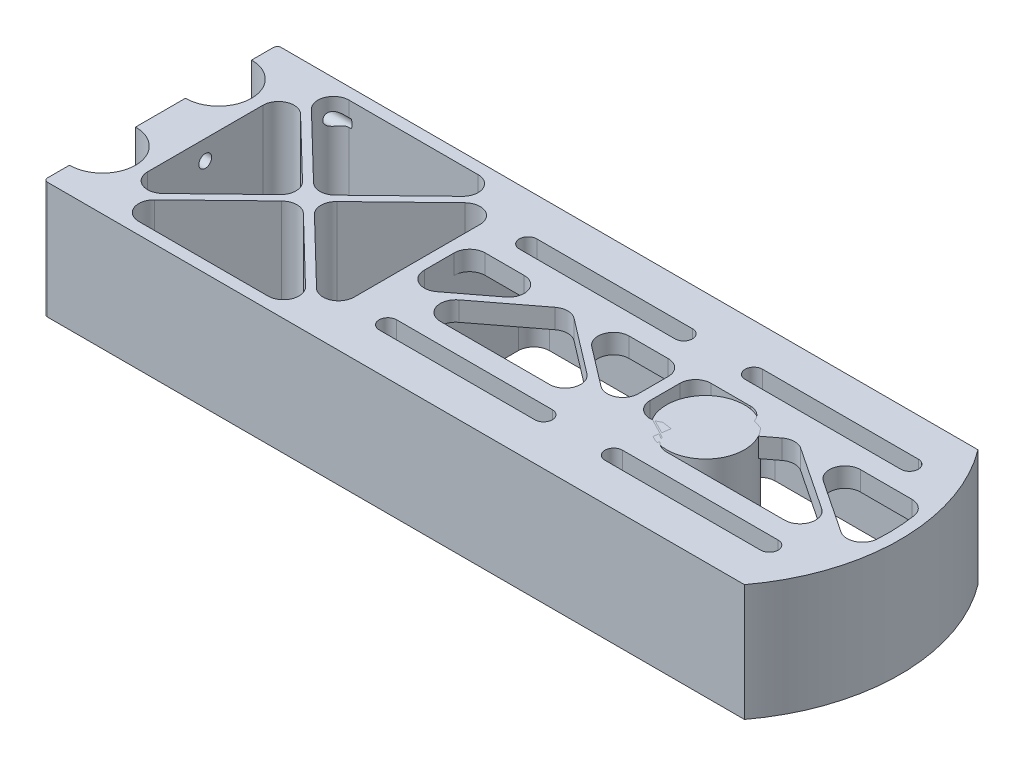
SolidWorks part; units mm, degrees
material "3.1355 (EN-AW 2024)"
ref_plane "Front" through (0, 0, 0) normal (0, 0, 1) x (1, 0, 0)
ref_plane "Top" through (0, 0, 0) normal (0, 1, 0) x (1, 0, 0)
ref_plane "Right" through (0, 0, 0) normal (1, 0, 0) x (0, 0, -1)
sketch "Эскиз1" plane through (0, 0, 0) normal (0, 1, 0) x (1, 0, 0)
  line L0 (0, 0) -> (0, 60) construction
  line L1 (0, 60) -> (180, 60)
  line L2 (190, 60) -> (190, 0) construction
  line L3 (190, 0) -> (180, 0) construction
  line L4 (0, 30) -> (140, 30) construction
  line L5 (0, 60) -> (0, 52)
  line L6 (0, 37.8) -> (0, 22.2)
  line L7 (0, 8) -> (0, 0)
  line L8 (140, 30) -> (190, 30) construction
  line L9 (180, 60) -> (190, 60) construction
  line L10 (180, 0) -> (0, 0)
  circle A0 centre (0, 44.9) radius 7.1 construction
  circle A1 centre (0, 15.1) radius 7.1 construction
  arc A2 (0, 52) -> (0, 37.8) centre (0, 44.9) cw
  arc A3 (0, 8) -> (0, 22.2) centre (0, 15.1) ccw
  arc A4 (180, 0) -> (180, 60) centre (140, 30) ccw
  point P11 (0, 52)
  point P12 (0, 37.8)
  dimension "D2" = 14.2
  dimension "D4" = 29.8
  dimension "D8" = 50
  dimension "D1" = 60
  dimension "D3" = 15.1
  dimension "D5" = 140
  dimension "D6" = 50
  dimension "D7" = 190
extrude "Бобышка-Вытянуть1" add sketch "Эскиз1" along normal blind 30
sketch "Эскиз2" plane through (0, 30, 0) normal (0, 1, 0) x (1, 0, 0)
  line L5 (3, 3) -> (178.4708, 3)
  line L6 (3, 3) -> (178.4708, 3)
  line L12 (3, 5.4558) -> (3, 3)
  line L15 (178.4708, 57) -> (3, 57)
  line L16 (3, 57) -> (3, 54.5442)
  line L17 (3, 35.2558) -> (3, 24.7442)
  line L18 (3, 5.4558) -> (3, 3)
  line L21 (178.4708, 57) -> (3, 57)
  line L22 (3, 57) -> (3, 54.5442)
  line L23 (3, 35.2558) -> (3, 24.7442)
  arc A3 (178.4708, 3) -> (178.4708, 57) centre (140, 30) ccw
  arc A4 (3, 35.2558) -> (3, 54.5442) centre (0, 44.9) ccw
  arc A5 (3, 5.4558) -> (3, 24.7442) centre (0, 15.1) ccw
  arc A6 (3, 35.2558) -> (3, 54.5442) centre (0, 44.9) ccw
  arc A7 (3, 5.4558) -> (3, 24.7442) centre (0, 15.1) ccw
  arc A8 (178.4708, 3) -> (178.4708, 57) centre (140, 30) ccw
  dimension "D1" = 3
extrude "Вырез-Вытянуть1" cut sketch "Эскиз2" against normal through all
sketch "Temp" plane through (0, 30, 0) normal (0, 1, 0) x (1, 0, 0)
  circle A0 centre (140, 30) radius 10
  dimension "D1" = 20
extrude "Бобышка-Вытянуть2" add sketch "Temp" against normal up to surface (30 mm away) separate body up to face at (49.7088, 0, -30)
sketch "Эскиз3" plane through (0, 30, 0) normal (0, 1, 0) x (1, 0, 0)
  line L0 (178.4708, 57) -> (3, 57) construction
  line L1 (174.4166, 48) -> (134.4166, 48) construction
  line L2 (174.4166, 43.5) -> (134.4166, 43.5)
  line L3 (174.4166, 52.5) -> (134.4166, 52.5)
  line L4 (174.4166, 48) -> (183.4166, 48) construction
  line L5 (125.4166, 57) -> (125.4166, 30) construction
  line L6 (0, 30) -> (140, 30) construction
  line L7 (76.4166, 48) -> (116.4166, 48) construction
  line L8 (76.4166, 43.5) -> (116.4166, 43.5)
  line L9 (76.4166, 52.5) -> (116.4166, 52.5)
  line L10 (187, 30) -> (125.4166, 30) construction
  line L11 (76.4166, 12) -> (116.4166, 12) construction
  line L12 (76.4166, 16.5) -> (116.4166, 16.5)
  line L13 (76.4166, 7.5) -> (116.4166, 7.5)
  line L14 (174.4166, 12) -> (134.4166, 12) construction
  line L15 (174.4166, 16.5) -> (134.4166, 16.5)
  line L16 (174.4166, 7.5) -> (134.4166, 7.5)
  line L17 (68.9166, 57) -> (68.9166, 40.5)
  line L18 (68.9166, 40.5) -> (185.8121, 40.5)
  line L19 (178.4708, 57) -> (68.9166, 57)
  line L20 (76.4166, 12) -> (116.4166, 12) construction
  line L21 (76.4166, 16.5) -> (116.4166, 16.5)
  line L22 (76.4166, 7.5) -> (116.4166, 7.5)
  line L23 (174.4166, 12) -> (134.4166, 12) construction
  line L24 (174.4166, 16.5) -> (134.4166, 16.5)
  line L25 (174.4166, 7.5) -> (134.4166, 7.5)
  line L26 (68.9166, 19.5) -> (185.8121, 19.5)
  line L27 (178.4708, 3) -> (68.9166, 3)
  line L28 (68.9166, 3) -> (68.9166, 19.5)
  arc A0 (174.4166, 43.5) -> (174.4166, 52.5) centre (174.4166, 48) ccw
  arc A1 (134.4166, 52.5) -> (134.4166, 43.5) centre (134.4166, 48) ccw
  arc A2 (178.4708, 3) -> (178.4708, 57) centre (140, 30) ccw construction
  arc A3 (76.4166, 43.5) -> (76.4166, 52.5) centre (76.4166, 48) cw
  arc A4 (116.4166, 52.5) -> (116.4166, 43.5) centre (116.4166, 48) cw
  arc A5 (76.4166, 16.5) -> (76.4166, 7.5) centre (76.4166, 12) ccw
  arc A6 (116.4166, 7.5) -> (116.4166, 16.5) centre (116.4166, 12) ccw
  arc A7 (174.4166, 16.5) -> (174.4166, 7.5) centre (174.4166, 12) cw
  arc A8 (134.4166, 7.5) -> (134.4166, 16.5) centre (134.4166, 12) cw
  arc A9 (185.8121, 40.5) -> (178.4708, 57) centre (140, 30) ccw
  arc A10 (76.4166, 16.5) -> (76.4166, 7.5) centre (76.4166, 12) ccw
  arc A11 (116.4166, 7.5) -> (116.4166, 16.5) centre (116.4166, 12) ccw
  arc A12 (174.4166, 16.5) -> (174.4166, 7.5) centre (174.4166, 12) cw
  arc A13 (134.4166, 7.5) -> (134.4166, 16.5) centre (134.4166, 12) cw
  arc A14 (185.8121, 19.5) -> (178.4708, 3) centre (140, 30) cw
  point P1 (154.4166, 48)
  point P20 (96.4166, 48)
  point P28 (96.4166, 12)
  point P35 (154.4166, 12)
  arc M3 (178.4708, 57) -> (178.4708, 3) centre (140, 30) cw
  line M4 (178.4708, 3) -> (3, 3)
  line M10 (3, 57) -> (178.4708, 57)
  dimension "D1" = 4.5
  dimension "D6" = 3
  dimension "D2" = 40
  dimension "D3" = 9
  dimension "D4" = 9
  dimension "D5" = 9
  dimension "D7" = 7.5
extrude "Бобышка-Вытянуть3" add sketch "Эскиз3" against normal blind 5 contours L17 L18 A1 L3 A0 L2 L9 A4 L8 A3 M3 M10 | L28 L26 A6 L13 A5 L12 L16 A8 L15 A7 M4 M3
sketch "Эскиз4" plane through (0, 30, 0) normal (0, 1, 0) x (1, 0, 0)
  line L0 (3, 57) -> (3, 54.5442) construction
  line L1 (3, 35.2558) -> (3, 24.7442) construction
  line L2 (3, 5.4558) -> (3, 3) construction
  line L3 (3, 3) -> (68.9166, 3) construction
  line L4 (68.9166, 57) -> (3, 57) construction
  line L5 (3, 57) -> (3, 54.5442)
  line L6 (3, 35.2558) -> (3, 24.7442)
  line L7 (3, 5.4558) -> (3, 3)
  line L8 (3, 3) -> (10.1, 3)
  line L9 (10.1, 57) -> (3, 57)
  line L10 (10.1, 57) -> (10.1, 3)
  arc A0 (3, 35.2558) -> (3, 54.5442) centre (0, 44.9) ccw construction
  arc A1 (3, 5.4558) -> (3, 24.7442) centre (0, 15.1) ccw construction
  arc A2 (3, 35.2558) -> (3, 54.5442) centre (0, 44.9) ccw
  arc A3 (3, 5.4558) -> (3, 24.7442) centre (0, 15.1) ccw
  line M4 (68.9166, 3) -> (3, 3)
  line M5 (3, 3) -> (3, 5.4558)
  arc M6 (3, 5.4558) -> (3, 24.7442) centre (0, 15.1) ccw
  line M7 (3, 24.7442) -> (3, 35.2558)
  arc M8 (3, 35.2558) -> (3, 54.5442) centre (0, 44.9) ccw
  line M9 (3, 54.5442) -> (3, 57)
  line M10 (3, 57) -> (68.9166, 57)
extrude "Бобышка-Вытянуть4" add sketch "Эскиз4" against normal through all contours L10 M10 M9 M8 | L10 M8 M7 M6 | L10 M6 M5 M4
sketch "Эскиз6" plane through (0, 30, 0) normal (0, 1, 0) x (1, 0, 0)
  line L0 (65.9166, 57) -> (65.9166, 3)
  line L1 (68.9166, 57) -> (10.1, 57) construction
  line L2 (10.1, 3) -> (68.9166, 3) construction
  line L3 (68.9166, 57) -> (68.9166, 40.5) construction
  line L4 (65.9166, 3) -> (68.9166, 3)
  line L5 (68.9166, 3) -> (68.9166, 57)
  line L6 (68.9166, 57) -> (65.9166, 57)
  dimension "D1" = 3
extrude "Бобышка-Вытянуть5" add sketch "Эскиз6" against normal through all
sketch "Эскиз7" plane through (0, 30, 0) normal (0, 1, 0) x (1, 0, 0)
  line L0 (10.1, 3) -> (65.9166, 57) construction
  line L1 (10.1, 57) -> (65.9166, 3) construction
  line L2 (10.1, 55.6086) -> (36.5701, 30)
  line L3 (11.5382, 3) -> (38.0083, 28.6086)
  line L4 (11.5382, 57) -> (38.0083, 31.3914)
  line L5 (10.1, 4.3914) -> (36.5701, 30)
  line L6 (65.9166, 57) -> (10.1, 57) construction
  line L7 (10.1, 57) -> (10.1, 3) construction
  line L8 (10.1, 3) -> (65.9166, 3) construction
  line L9 (65.9166, 57) -> (65.9166, 3) construction
  line L10 (65.9166, 57) -> (64.4784, 57)
  line L11 (10.1, 57) -> (10.1, 55.6086)
  line L12 (10.1, 3) -> (11.5382, 3)
  line L13 (65.9166, 57) -> (65.9166, 55.6086)
  line L14 (11.5382, 57) -> (10.1, 57)
  line L15 (10.7953, 57.7187) -> (66.6119, 3.7187) construction
  line L16 (9.4047, 56.2813) -> (65.2213, 2.2813) construction
  line L17 (65.9166, 4.3914) -> (65.9166, 3)
  line L18 (9.4047, 3.7187) -> (65.2213, 57.7187) construction
  line L19 (10.7953, 2.2813) -> (66.6119, 56.2813) construction
  line L20 (64.4784, 3) -> (65.9166, 3)
  line L21 (10.1, 4.3914) -> (10.1, 3)
  line L22 (39.4465, 30) -> (65.9166, 55.6086)
  line L23 (39.4465, 30) -> (65.9166, 4.3914)
  line L24 (38.0083, 31.3914) -> (64.4784, 57)
  line L25 (38.0083, 28.6086) -> (64.4784, 3)
  dimension "D1" = 1
  dimension "D2" = 1
extrude "Бобышка-Вытянуть6" add sketch "Эскиз7" against normal through all
sketch "Эскиз9" plane through (0, 25, 0) normal (0, -1, 0) x (1, 0, 0)
  line L0 (120.9166, -12) -> (129.9166, -12) construction
  line L1 (125.4166, -3) -> (125.4166, -57) construction
  line L2 (68.9166, -57) -> (178.4708, -57) construction
  line L3 (123.9166, -3) -> (123.9166, -57)
  line L4 (101.5292, -3) -> (68.9166, -3) construction
  line L5 (126.9166, -3) -> (126.9166, -57)
  line L6 (123.9166, -3) -> (126.9166, -3)
  line L7 (123.9166, -57) -> (126.9166, -57)
  arc A0 (116.4166, -16.5) -> (116.4166, -7.5) centre (116.4166, -12) ccw construction
  arc A1 (134.4166, -16.5) -> (134.4166, -7.5) centre (134.4166, -12) ccw construction
  point P8 (125.4166, -12)
  dimension "D1" = 1.5
  dimension "D2" = 1.5
extrude "Бобышка-Вытянуть8" add sketch "Эскиз9" along normal through all and the other way through all
sketch "Эскиз8" plane through (0, 30, 0) normal (0, 1, 0) x (1, 0, 0)
  line L0 (96.4166, 43.5) -> (96.4166, 16.5) construction
  line L1 (76.4166, 43.5) -> (116.4166, 43.5) construction
  line L2 (76.4166, 16.5) -> (116.4166, 16.5) construction
  line L3 (154.4166, 43.5) -> (154.4166, 16.5) construction
  line L4 (174.4166, 43.5) -> (134.4166, 43.5) construction
  line L5 (174.4166, 16.5) -> (134.4166, 16.5) construction
  line L6 (68.9166, 19.5) -> (96.4166, 40.5) construction
  line L7 (116.4166, 48) -> (134.4166, 48) construction
  line L8 (125.4166, 48) -> (125.4166, 19.5) construction
  line L9 (68.9166, 40.5) -> (123.9166, 40.5) construction
  line L10 (96.4166, 40.5) -> (123.9166, 19.5) construction
  line L11 (126.9166, 19.5) -> (154.4401, 40.4052) construction
  line L12 (154.4401, 40.4052) -> (185.8121, 19.5) construction
  line L13 (70.5643, 19.5) -> (96.4166, 39.2418)
  line L14 (96.4166, 39.2418) -> (122.2689, 19.5)
  line L15 (128.5699, 19.5) -> (154.478, 39.1782)
  line L16 (154.478, 39.1782) -> (184.0088, 19.5)
  line L17 (68.9166, 20.7582) -> (94.7689, 40.5)
  line L18 (98.0643, 40.5) -> (123.9166, 20.7582)
  line L19 (126.9166, 20.7557) -> (152.9116, 40.5)
  line L20 (122.2689, 19.5) -> (123.9166, 19.5)
  line L22 (94.7689, 40.5) -> (98.0643, 40.5)
  line L23 (68.9166, 19.5) -> (68.9166, 40.5) construction
  line L24 (68.9166, 19.5) -> (123.9166, 19.5) construction
  line L25 (123.9166, 19.5) -> (123.9166, 40.5) construction
  line L26 (126.9166, 40.5) -> (126.9166, 19.5) construction
  line L27 (126.9166, 40.5) -> (185.8121, 40.5) construction
  line L28 (126.9166, 19.5) -> (185.8121, 19.5) construction
  line L29 (68.9166, 19.5) -> (68.9166, 20.7582)
  line L30 (68.9166, 19.5) -> (70.5643, 19.5)
  line L31 (123.9166, 19.5) -> (123.9166, 20.7582)
  line L32 (126.9166, 20.7557) -> (126.9166, 19.5)
  line L33 (152.9116, 40.5) -> (156.1011, 40.5)
  line L34 (126.9166, 19.5) -> (128.5699, 19.5)
  line L35 (184.0088, 19.5) -> (185.8121, 19.5)
  line L36 (154.4021, 41.6321) -> (186.3666, 20.3322) construction
  line L37 (154.478, 39.1782) -> (185.2576, 18.6678) construction
  line L38 (156.1011, 40.5) -> (186.0401, 20.5497)
  line L39 (127.5214, 18.7037) -> (154.478, 39.1782) construction
  line L40 (126.3117, 20.2963) -> (154.4021, 41.6321) construction
  line L42 (96.4166, 41.7582) -> (124.5235, 20.2948) construction
  line L43 (68.3097, 20.2948) -> (96.4166, 41.7582) construction
  line L44 (69.5235, 18.7052) -> (96.4166, 39.2418) construction
  line L45 (96.4166, 39.2418) -> (123.3097, 18.7052) construction
  arc A1 (185.8121, 19.5) -> (185.8121, 40.5) centre (140, 30) ccw construction
  arc A2 (185.8121, 19.5) -> (186.0401, 20.5497) centre (140, 30) ccw
  point P26 (69.5235, 18.7052)
  point P27 (96.4324, 39.2539)
  point P28 (125.4324, 18.2539)
  point P30 (185.2357, 18.6828)
  point P31 (68.3097, 20.2948)
  point P32 (96.4007, 41.7461)
  point P33 (125.4007, 20.7461)
  point P34 (154.3931, 42.8858)
  point P35 (186.3885, 20.3172)
  point P49 (154.4166, 40.5)
  dimension "D1" = 1
  dimension "D2" = 1
extrude "Бобышка-Вытянуть7" add sketch "Эскиз8" against normal up to surface (5 mm away) up to face at (96.4166, 25, -12)
fillet "Скругление1" radius 4 10 edges at (11.5382, 15, -57) (38.0083, 15, -31.3914) (64.4784, 15, -57) (65.9166, 15, -55.6086) (39.4465, 15, -30) (65.9166, 15, -4.3914) (11.5382, 15, -3) (64.4784, 15, -3) (38.0083, 15, -28.6086) (36.5701, 15, -30)
fillet "Скругление2" radius 4 8 edges at (178.4708, 12.5, -57) (178.4708, 12.5, -3) (126.9166, 12.5, -3) (126.9166, 12.5, -57) (123.9166, 12.5, -3) (68.9166, 12.5, -3) (68.9166, 12.5, -57) (123.9166, 12.5, -57)
fillet "Скругление3" radius 4 18 edges at (98.0643, 27.5, -40.5) (123.9166, 27.5, -40.5) (123.9166, 27.5, -20.7582) (122.2689, 27.5, -19.5) (96.4166, 27.5, -39.2418) (70.5643, 27.5, -19.5) (94.7689, 27.5, -40.5) (68.9166, 27.5, -40.5) (68.9166, 27.5, -20.7582) (185.8121, 27.5, -40.5) (156.1011, 27.5, -40.5) (186.0401, 27.5, -20.5497) (184.0088, 27.5, -19.5) (154.478, 27.5, -39.1782) (128.5699, 27.5, -19.5) (126.9166, 27.5, -20.7557) (152.9116, 27.5, -40.5) (126.9166, 27.5, -40.5)
sketch "Эскиз10" plane through (0, 30, 0) normal (0, 1, 0) x (1, 0, 0)
  line L90 (76.4166, 52.5) -> (116.4166, 52.5) construction
  line L91 (76.4166, 43.5) -> (116.4166, 43.5) construction
  line L92 (116.4166, 50.25) -> (76.4166, 50.25)
  line L93 (76.4166, 45.75) -> (116.4166, 45.75)
  line L94 (116.4166, 50.25) -> (76.4166, 50.25)
  line L95 (76.4166, 45.75) -> (116.4166, 45.75)
  line L96 (76.4166, 52.5) -> (116.4166, 52.5)
  line L97 (76.4166, 43.5) -> (116.4166, 43.5)
  line L98 (174.4166, 52.5) -> (134.4166, 52.5) construction
  line L99 (174.4166, 43.5) -> (134.4166, 43.5) construction
  line L100 (174.4166, 52.5) -> (134.4166, 52.5)
  line L101 (174.4166, 43.5) -> (134.4166, 43.5)
  line L102 (76.4166, 16.5) -> (116.4166, 16.5) construction
  line L103 (76.4166, 7.5) -> (116.4166, 7.5) construction
  line L104 (76.4166, 16.5) -> (116.4166, 16.5)
  line L105 (76.4166, 7.5) -> (116.4166, 7.5)
  line L106 (174.4166, 16.5) -> (134.4166, 16.5) construction
  line L107 (174.4166, 7.5) -> (134.4166, 7.5) construction
  line L108 (174.4166, 16.5) -> (134.4166, 16.5)
  line L109 (174.4166, 7.5) -> (134.4166, 7.5)
  line L110 (174.4166, 45.75) -> (134.4166, 45.75)
  line L111 (174.4166, 50.25) -> (134.4166, 50.25)
  line L112 (174.4166, 14.25) -> (134.4166, 14.25)
  line L113 (174.4166, 9.75) -> (134.4166, 9.75)
  line L114 (76.4166, 9.75) -> (116.4166, 9.75)
  line L115 (76.4166, 14.25) -> (116.4166, 14.25)
  arc A90 (76.4166, 52.5) -> (76.4166, 43.5) centre (76.4166, 48) ccw construction
  arc A91 (116.4166, 43.5) -> (116.4166, 52.5) centre (116.4166, 48) ccw construction
  arc A92 (76.4166, 50.25) -> (76.4166, 45.75) centre (76.4166, 48) ccw
  arc A93 (116.4166, 45.75) -> (116.4166, 50.25) centre (116.4166, 48) ccw
  arc A94 (76.4166, 50.25) -> (76.4166, 45.75) centre (76.4166, 48) ccw
  arc A95 (116.4166, 45.75) -> (116.4166, 50.25) centre (116.4166, 48) ccw
  arc A96 (76.4166, 52.5) -> (76.4166, 43.5) centre (76.4166, 48) ccw
  arc A97 (116.4166, 43.5) -> (116.4166, 52.5) centre (116.4166, 48) ccw
  arc A98 (134.4166, 52.5) -> (134.4166, 43.5) centre (134.4166, 48) ccw construction
  arc A99 (174.4166, 43.5) -> (174.4166, 52.5) centre (174.4166, 48) ccw construction
  arc A100 (134.4166, 52.5) -> (134.4166, 43.5) centre (134.4166, 48) ccw
  arc A101 (174.4166, 43.5) -> (174.4166, 52.5) centre (174.4166, 48) ccw
  arc A102 (116.4166, 7.5) -> (116.4166, 16.5) centre (116.4166, 12) ccw construction
  arc A103 (76.4166, 16.5) -> (76.4166, 7.5) centre (76.4166, 12) ccw construction
  arc A104 (116.4166, 7.5) -> (116.4166, 16.5) centre (116.4166, 12) ccw
  arc A105 (76.4166, 16.5) -> (76.4166, 7.5) centre (76.4166, 12) ccw
  arc A106 (134.4166, 16.5) -> (134.4166, 7.5) centre (134.4166, 12) ccw construction
  arc A107 (174.4166, 7.5) -> (174.4166, 16.5) centre (174.4166, 12) ccw construction
  arc A108 (134.4166, 16.5) -> (134.4166, 7.5) centre (134.4166, 12) ccw
  arc A109 (174.4166, 7.5) -> (174.4166, 16.5) centre (174.4166, 12) ccw
  arc A110 (134.4166, 50.25) -> (134.4166, 45.75) centre (134.4166, 48) ccw
  arc A111 (174.4166, 45.75) -> (174.4166, 50.25) centre (174.4166, 48) ccw
  arc A112 (134.4166, 14.25) -> (134.4166, 9.75) centre (134.4166, 12) ccw
  arc A113 (174.4166, 9.75) -> (174.4166, 14.25) centre (174.4166, 12) ccw
  arc A114 (76.4166, 14.25) -> (76.4166, 9.75) centre (76.4166, 12) ccw
  arc A115 (116.4166, 9.75) -> (116.4166, 14.25) centre (116.4166, 12) ccw
  dimension "D1" = 2.25
  dimension "D2" = 2.25
  dimension "D3" = 2.25
  dimension "D4" = 2.25
extrude "Бобышка-Вытянуть9" add sketch "Эскиз10" against normal up to surface (5 mm away) up to face at (155.2427, 25, -27.7696)
sketch "Эскиз12" plane through (0, 0, 0) normal (0, -1, 0) x (1, 0, 0)
  line L0 (5, -23.8755) -> (5, -36.1245)
  line L1 (0, -37.8) -> (0, -22.2) construction
  line L2 (10.1, -55.6086) -> (10.1, -4.3914) construction
  line L3 (10.1, -44.9) -> (10.1, -15.1)
  arc A6 (0, -25.2) -> (0, -5) centre (0, -15.1) ccw
  arc A7 (5, -23.8755) -> (10.1, -15.1) centre (0, -15.1) ccw
  arc A9 (0, -55) -> (0, -34.8) centre (0, -44.9) ccw
  arc A10 (10.1, -44.9) -> (5, -36.1245) centre (0, -44.9) ccw
  dimension "D3" = 5
  dimension "D1" = 3
  dimension "D2" = 3
extrude "Вырез-Вытянуть2" [suppressed] cut sketch "Эскиз12" against normal through all
sketch "Эскиз15" [suppressed] plane through (0, 0, 0) normal (0, -1, 0) x (1, 0, 0)
  line L5 (180, 0) -> (0, 0)
  line L6 (0, 0) -> (0, -8)
  line L7 (0, -22.2) -> (0, -37.8)
  line L8 (0, -52) -> (0, -60)
  line L9 (0, -60) -> (180, -60)
  line L10 (180, 0) -> (0, 0)
  line L11 (0, 0) -> (0, -8)
  line L12 (0, -22.2) -> (0, -37.8)
  line L13 (0, -52) -> (0, -60)
  line L14 (0, -60) -> (180, -60)
  arc A3 (0, -22.2) -> (0, -8) centre (0, -15.1) ccw
  arc A4 (0, -52) -> (0, -37.8) centre (0, -44.9) ccw
  arc A5 (180, -60) -> (180, 0) centre (140, -30) ccw
  arc A6 (0, -22.2) -> (0, -8) centre (0, -15.1) ccw
  arc A7 (0, -52) -> (0, -37.8) centre (0, -44.9) ccw
  arc A8 (180, -60) -> (180, 0) centre (140, -30) ccw
  dimension "D1" = 0
extrude "Вырез-Вытянуть3" [suppressed] cut sketch "Эскиз15" against normal blind 20
split "Разделить1" [suppressed] bodies to split 113
move or copy body "Тело-Переместить/Копировать1" [suppressed] bodies to move or copy 116 placed by mates yes
other "Расстояние2" [suppressed] parameters "D1"=50
sketch "Эскиз16" plane through (0, 30, 0) normal (0, 1, 0) x (1, 0, 0)
  line L0 (0, 8) -> (0, 0) construction
  line L1 (0, 37.8) -> (0, 22.2) construction
  line L2 (0, 60) -> (0, 52) construction
  line L3 (0, 8) -> (0, 6.6)
  line L4 (0, 37.8) -> (0, 36.4)
  line L5 (0, 53.4) -> (0, 52)
  line L6 (0, 23.6) -> (0, 22.2)
  arc A3 (0, 36.4) -> (0, 53.4) centre (0, 44.9) ccw
  arc A4 (0, 36.4) -> (0, 53.4) centre (0, 44.9) ccw
  arc A5 (0, 37.8) -> (0, 52) centre (0, 44.9) ccw construction
  arc A6 (0, 6.6) -> (0, 23.6) centre (0, 15.1) ccw
  arc A7 (0, 6.6) -> (0, 23.6) centre (0, 15.1) ccw
  arc A8 (0, 8) -> (0, 22.2) centre (0, 15.1) ccw construction
  arc A9 (0, 37.8) -> (0, 52) centre (0, 44.9) ccw
  arc A10 (0, 8) -> (0, 22.2) centre (0, 15.1) ccw
  dimension "D1" = 1.4
  dimension "D2" = 1.4
extrude "Вырез-Вытянуть4" cut sketch "Эскиз16" against normal through all
sketch "Эскиз17" plane through (0, 30, 0) normal (0, 1, 0) x (1, 0, 0)
  line L1 (10.1, 55.6086) -> (10.1, 4.3914) construction
  line L2 (11.5, 55.6086) -> (11.5, 4.3914)
  line L3 (11.5, 54.2542) -> (11.5, 5.7458)
  line L4 (10.1, 55.6086) -> (33.5986, 32.8748) construction
  line L5 (33.5986, 27.1252) -> (10.1, 4.3914) construction
  line L6 (10.1, 55.6086) -> (10.1, 4.3914)
  line L7 (10.1, 55.6086) -> (11.5, 54.2542)
  line L8 (11.5, 5.7458) -> (10.1, 4.3914)
  dimension "D1" = 1.4
extrude "Бобышка-Вытянуть10" add sketch "Эскиз17" against normal through all
fillet "Скругление4" radius 4 2 edges at (11.5, 15, -54.2542) (11.5, 15, -5.7458)
hole_wizard "Отверстие обработанное метчиком M4x0.71" positions "Эскиз13" profile "Эскиз14" tap size "M4x0.7" standard "Ansi Metric"
sketch "Эскиз13" plane through (0, -175.3797, -75.0604) normal (-1, 0, 0) x (0, 0, 1)
  point P0 (19.3104, 200.3797)
  point P3 (45.0604, 200.3797)
  point P6 (70.8104, 200.3797)
  point P9 (70.8104, 180.3797)
  point P12 (45.0604, 180.3797)
  point P15 (19.3104, 180.3797)
sketch "Эскиз14" plane through (0, 25, -55.75) normal (0, 1, 0) x (0, 0, 1)
  line L0 (0, 0) -> (0, 22.9914)
  line L1 (0, 22.9914) -> (1.65, 22)
  line L2 (1.65, 22) -> (1.65, 0)
  line L3 (1.65, 0) -> (0, 0)
  line L4 (0, 22.9914) -> (-1.65, 22) construction
  line L5 (0, -6.35) -> (0, 107.95) construction
  dimension "Диаметр сверла" = 3.3
  dimension "Глубина сверла" = 22
  dimension "Угол заточки сверла" = 118
cosmetic thread "Отверстие резьбы1" parameters "D1"=22, "D2"=4
cosmetic thread "Отверстие резьбы2" parameters "D1"=11.5, "D2"=4
cosmetic thread "Отверстие резьбы3" parameters "D1"=22, "D2"=4
cosmetic thread "Отверстие резьбы4" parameters "D1"=22, "D2"=4
cosmetic thread "Отверстие резьбы5" parameters "D1"=11.5, "D2"=4
cosmetic thread "Отверстие резьбы6" parameters "D1"=22, "D2"=4
fillet "Скругление5" radius 1 2 edges at (0, 15, 0) (0, 15, -60)
equation "\"D3@Эскиз1\"=8+\"D2@Эскиз1\"/2"
equation "\"D7@Эскиз3\"=\"D1@Эскиз3\"+3"
